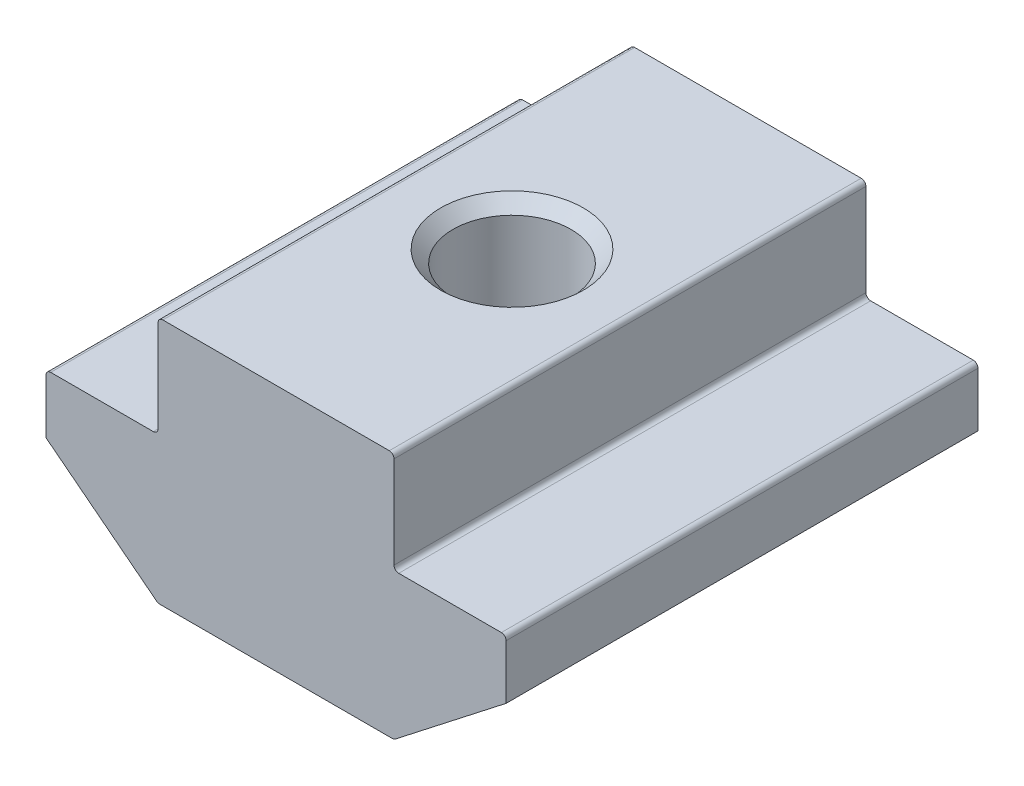
SolidWorks part; units mm, degrees
ref_plane "Спереди" through (0, 0, 0) normal (0, 0, 1) x (1, 0, 0)
ref_plane "Сверху" through (0, 0, 0) normal (0, 1, 0) x (1, 0, 0)
ref_plane "Справа" through (0, 0, 0) normal (1, 0, 0) x (0, 0, -1)
sketch "Эскиз1" plane through (0, 0, 0) normal (0, 0, 1) x (1, 0, 0)
  line L0 (5, 0) -> (-5, 0)
  line L1 (-5, 0) -> (-5, -4.3)
  line L2 (-5, -4.3) -> (-9.75, -4.3)
  line L3 (-9.75, -4.3) -> (-9.75, -6.8)
  line L4 (-9.75, -6.8) -> (-5, -10.5)
  line L5 (-5, -10.5) -> (5, -10.5)
  line L6 (0, -10.5) -> (0, 0) construction
  line L7 (9.75, -6.8) -> (5, -10.5)
  line L8 (9.75, -4.3) -> (9.75, -6.8)
  line L9 (5, -4.3) -> (9.75, -4.3)
  line L10 (5, 0) -> (5, -4.3)
  point P3 (-5, -2.15)
  dimension "D1" = 10
  dimension "D2" = 19.5
  dimension "D3" = 2.5
  dimension "D4" = 10.5
  dimension "D5" = 6.2
extrude "Бобышка-Вытянуть1" add sketch "Эскиз1" along normal mid plane 20
hole_wizard "Отверстие обработанное метчиком M64" positions "Эскиз2" profile "Эскиз4" tap size "M6" standard "ISO" end condition through all
sketch "Эскиз2" plane through (0, 0, 0) normal (0, 1, 0) x (1, 0, 0)
  point P0 (0, 0)
sketch "Эскиз4" plane through (0, 0, 0) normal (1, 0, 0) x (0, 0, 1)
  line L0 (0, 0) -> (0, 10.5)
  line L1 (0, 10.5) -> (3.025, 10.5)
  line L2 (2.5, 9.975) -> (2.5, 0.525)
  line L3 (2.5, 0.525) -> (3.025, 0)
  line L5 (3.025, 0) -> (0, 0)
  line L6 (-2.5, 0.525) -> (-3.025, 0) construction
  line L7 (3.025, 10.5) -> (2.5, 9.975)
  line L8 (-3.025, 10.5) -> (-2.5, 9.975) construction
  line L11 (0, -6.35) -> (0, 107.95) construction
  dimension "Диаметр проходного сверла" = 5
  dimension "Глубина проходного сверла" = 10.5
  dimension "Диаметр передней зенковки" = 6.05
  dimension "Угол передней зенковки" = 90
  dimension "Диаметр задней зенковки" = 6.05
  dimension "Угол задней зенковки" = 90
cosmetic thread "Отверстие резьбы1" parameters "D2"=6
fillet "Скругление1" radius 0.2 8 edges at (5, -10.5, 0) (-5, -10.5, 0) (9.75, -4.3, 0) (5, -4.3, 0) (5, 0, 0) (-5, 0, 0) (-9.75, -4.3, 0) (-5, -4.3, 0)
